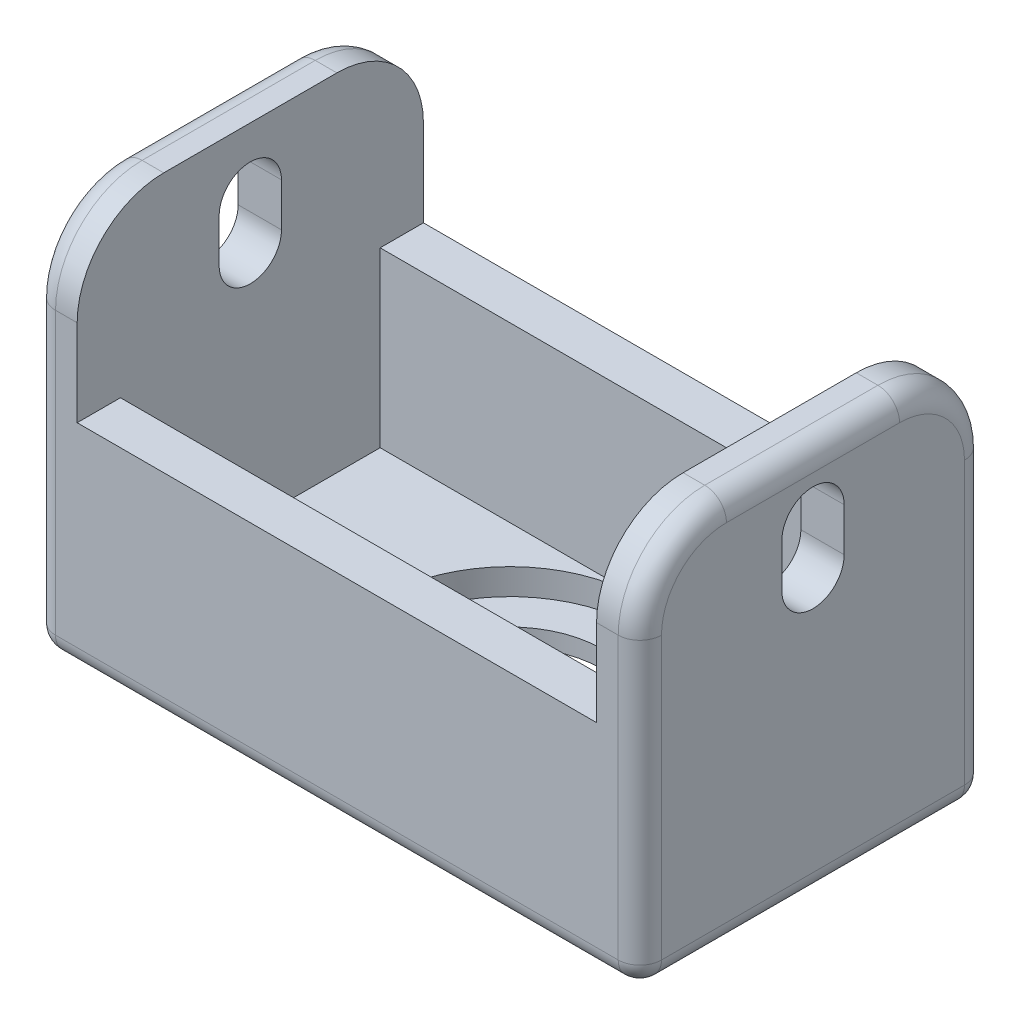
SolidWorks part; units mm, degrees
ref_plane "Front Plane" through (0, 0, 0) normal (0, 0, 1) x (1, 0, 0)
ref_plane "Top Plane" through (0, 0, 0) normal (0, 1, 0) x (1, 0, 0)
ref_plane "Right Plane" through (0, 0, 0) normal (1, 0, 0) x (0, 0, -1)
sketch "Sketch1" plane through (0, 0, 0) normal (0, 1, 0) x (1, 0, 0)
  line L1 (0, 0) -> (44.45, 0)
  line L2 (0, 0) -> (0, 25.4)
  line L3 (0, 25.4) -> (44.45, 25.4)
  line L4 (44.45, 0) -> (44.45, 25.4)
  dimension "D1" = 44.45
  dimension "D2" = 25.4
extrude "Boss-Extrude1" add sketch "Sketch1" along normal blind 28.575
shell "Shell1" thickness 3.175
sketch "Sketch2" plane through (0, 0, 0) normal (0, 0, 1) x (1, 0, 0)
  line L0 (0, 28.575) -> (44.45, 28.575) construction
  line L1 (3.175, 28.575) -> (41.275, 28.575)
  line L2 (3.175, 28.575) -> (3.175, 15.875)
  line L3 (3.175, 15.875) -> (41.275, 15.875)
  line L4 (41.275, 28.575) -> (41.275, 15.875)
  line L5 (0, 0) -> (44.45, 0) construction
  point P8 (22.225, 0)
  point P9 (22.225, 15.875)
  dimension "D1" = 12.7
  dimension "D2" = 38.1
extrude "Cut-Extrude1" cut sketch "Sketch2" against normal through all
sketch "Sketch3" plane through (0, 0, 0) normal (-1, 0, 0) x (0, 0, 1)
  line L0 (-12.7, 23.8125) -> (-12.7, 20.6375) construction
  line L1 (-10.414, 23.8125) -> (-10.414, 20.6375)
  line L2 (-14.986, 23.8125) -> (-14.986, 20.6375)
  line L3 (-25.4, 28.575) -> (0, 28.575) construction
  line L4 (-25.4, 0) -> (0, 0) construction
  arc A0 (-10.414, 23.8125) -> (-14.986, 23.8125) centre (-12.7, 23.8125) ccw
  arc A1 (-14.986, 20.6375) -> (-10.414, 20.6375) centre (-12.7, 20.6375) ccw
  point P2 (-12.7, 22.225)
  point P11 (-12.7, 0)
  dimension "D1" = 2.286
  dimension "D2" = 6.35
  dimension "D3" = 3.175
extrude "Cut-Extrude2" cut sketch "Sketch3" against normal through all
sketch "Sketch5" plane through (0, 3.175, 0) normal (0, 1, 0) x (1, 0, 0)
  line L0 (25.1997, 6.5913) -> (19.2503, 6.5913)
  line L1 (41.275, 3.175) -> (41.275, 22.225) construction
  line L2 (41.275, 22.225) -> (3.175, 22.225) construction
  arc A0 (25.1997, 6.5913) -> (19.2503, 6.5913) centre (22.225, 12.7) ccw
  point P1 (22.225, 19.4945)
  point P6 (41.275, 12.7)
  point P9 (22.225, 22.225)
  dimension "D1" = 13.589
  dimension "D2" = 12.9032
extrude "Cut-Extrude3" cut sketch "Sketch5" against normal through all
fillet "Fillet1" radius 6.35 4 edges at (1.5875, 28.575, -25.4) (1.5875, 28.575, 0) (42.8625, 28.575, -25.4) (42.8625, 28.575, 0)
fillet "Fillet2" radius 1.5875 14 edges at (44.45, 11.1125, -25.4) (44.45, 26.7151, -23.5401) (44.45, 28.575, -12.7) (44.45, 26.7151, -1.8599) (0, 11.1125, -25.4) (0, 26.7151, -23.5401) (0, 28.575, -12.7) (0, 26.7151, -1.8599) (22.225, 0, 0) (44.45, 0, -12.7) (22.225, 0, -25.4) (0, 0, -12.7) (44.45, 11.1125, 0) (0, 11.1125, 0)
sketch "Sketch6" plane through (0, 3.175, 0) normal (0, 1, 0) x (1, 0, 0)
  line L0 (41.275, 3.175) -> (3.175, 3.175) construction
  circle A0 centre (22.225, 12.7) radius 9.525
  arc A1 (25.1997, 6.5913) -> (19.2503, 6.5913) centre (22.225, 12.7) ccw construction
extrude "Cut-Extrude4" cut sketch "Sketch6" against normal blind 1.905
